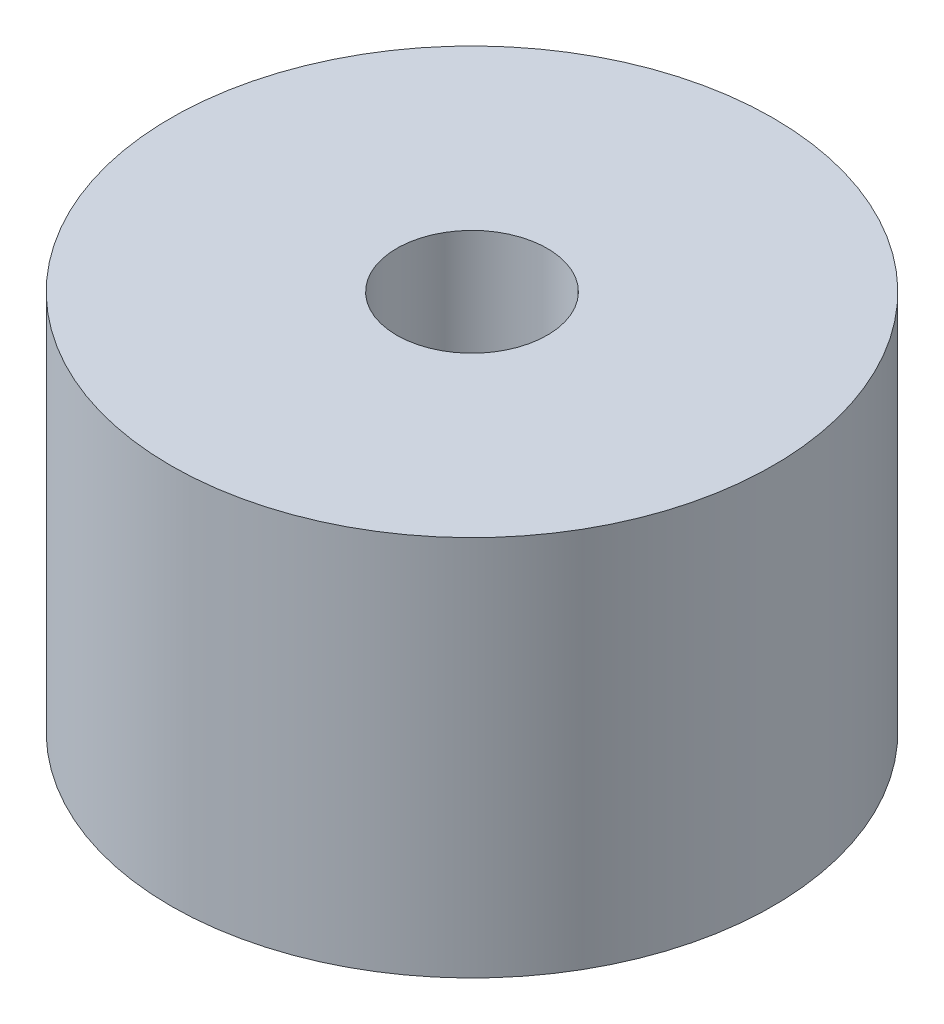
SolidWorks part; units mm, degrees
ref_plane "Přední rovina" through (0, 0, 0) normal (0, 0, 1) x (1, 0, 0)
ref_plane "Horní rovina" through (0, 0, 0) normal (0, 1, 0) x (1, 0, 0)
ref_plane "Pravá rovina" through (0, 0, 0) normal (1, 0, 0) x (0, 0, -1)
sketch "Skica1" plane through (0, 0, 0) normal (0, 1, 0) x (1, 0, 0)
  circle A0 centre (0, 0) radius 6
  dimension "D1" = 12
extrude "Přidat vysunutím1" add sketch "Skica1" along normal blind 7.6
sketch "Skica2" plane through (0, 7.6, 0) normal (0, 1, 0) x (1, 0, 0)
  circle A0 centre (0, 0) radius 1.5
  dimension "D1" = 3
extrude "Odebrat vysunutím1" cut sketch "Skica2" against normal blind 4
